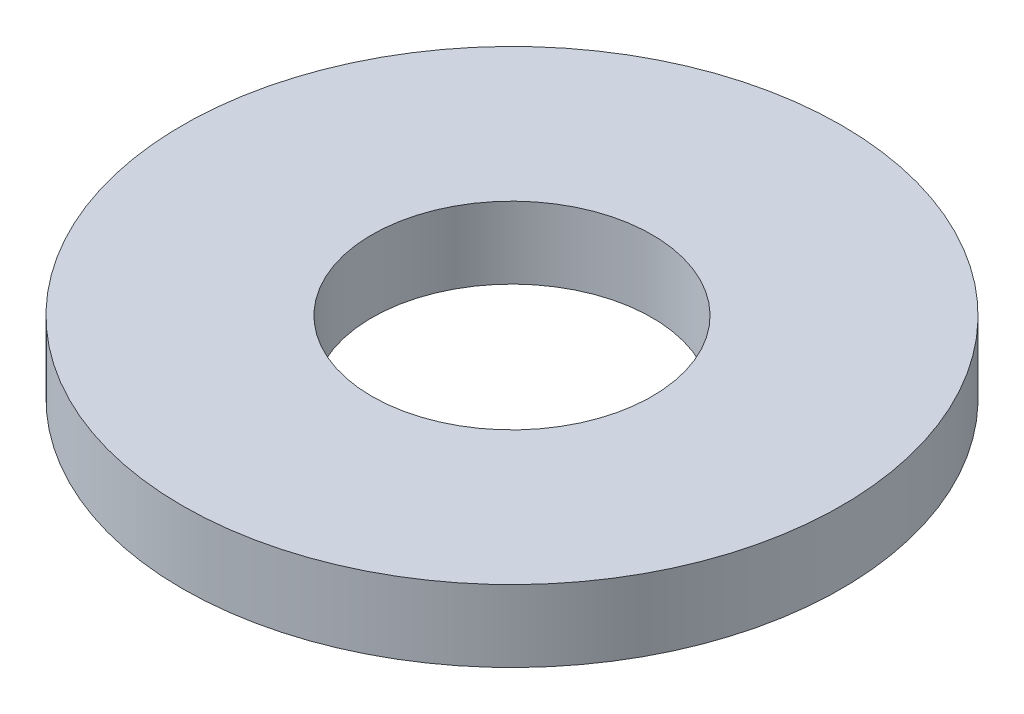
SolidWorks part; units mm, degrees
ref_plane "Front Plane" through (0, 0, 0) normal (0, 0, 1) x (1, 0, 0)
ref_plane "Top Plane" through (0, 0, 0) normal (0, 1, 0) x (1, 0, 0)
ref_plane "Right Plane" through (0, 0, 0) normal (1, 0, 0) x (0, 0, -1)
sketch "Sketch1" plane through (0, 0, 0) normal (0, 1, 0) x (1, 0, 0)
  circle A0 centre (0, 0) radius 9.3218
  dimension "OD" = 18.6436
extrude "Boss-Extrude1" add sketch "Sketch1" along normal blind 2.032
sketch "Sketch5" plane through (0, 2.032, 0) normal (0, 1, 0) x (-1, 0, 0)
  circle A0 centre (0, 0) radius 3.9624
  dimension "ID" = 7.9248
extrude "Cut-Extrude1" cut sketch "Sketch5" against normal through all
